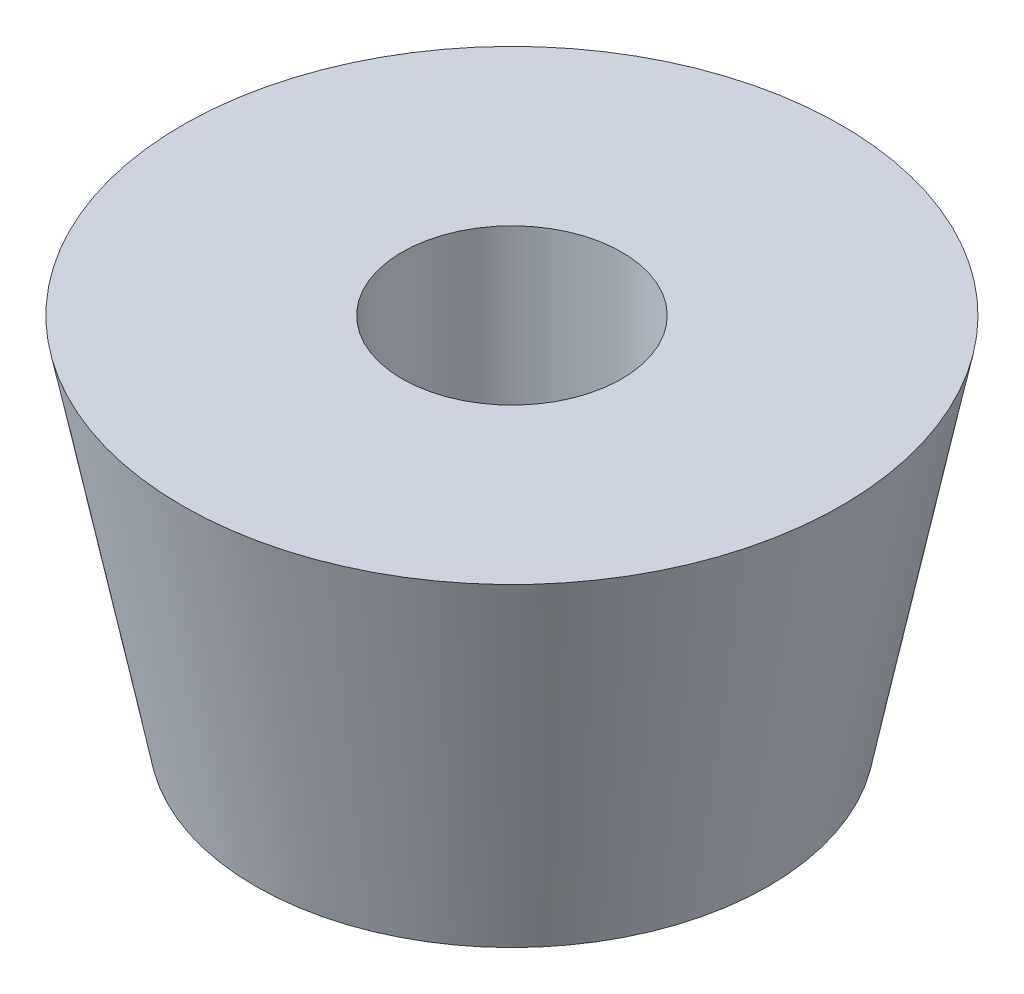
SolidWorks part; units mm, degrees
ref_plane "Front Plane" through (0, 0, 0) normal (0, 0, 1) x (1, 0, 0)
ref_plane "Top Plane" through (0, 0, 0) normal (0, 1, 0) x (1, 0, 0)
ref_plane "Right Plane" through (0, 0, 0) normal (1, 0, 0) x (0, 0, -1)
sketch "Sketch1" plane through (0, 0, 0) normal (1, 0, 0) x (0, 0, -1)
  line L0 (0, 0) -> (0, -2.7386) construction
  line L1 (1.5, 0) -> (4.5, 0)
  line L2 (4.5, 0) -> (3.5, -5)
  line L3 (3.5, -5) -> (1.5, -5)
  line L4 (1.5, -5) -> (1.5, 0)
  point P5 (2.5, -5)
  dimension "D1" = 3
  dimension "D2" = 2
  dimension "D3" = 1.5
  dimension "D4" = 5
revolve "Revolve1" add sketch "Sketch1" angle 360 about L0
